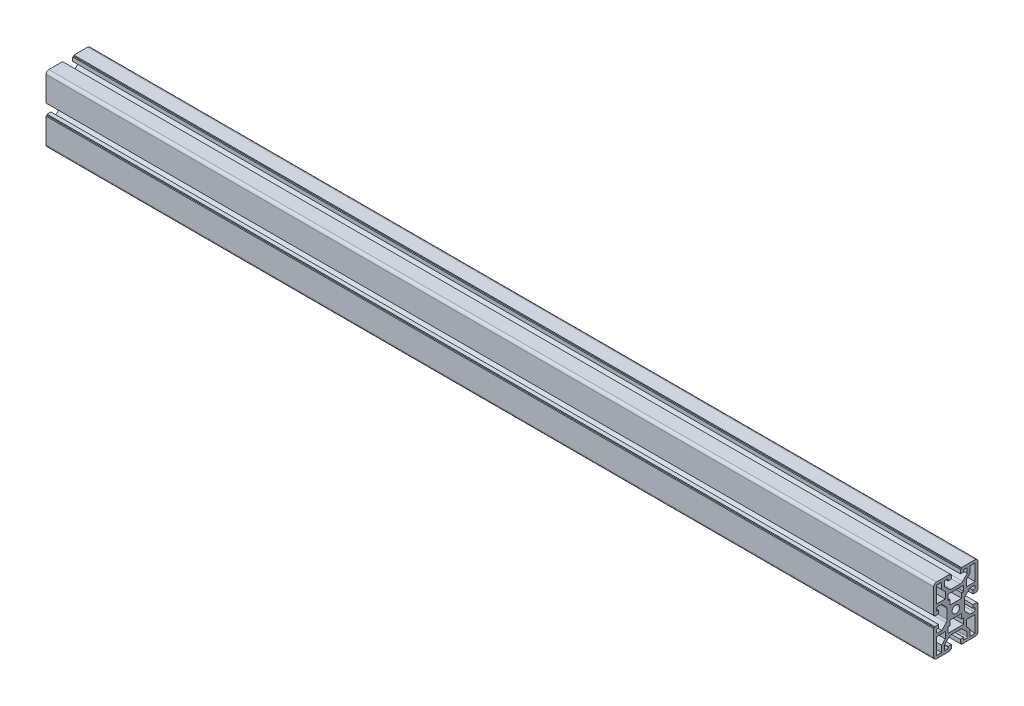
SolidWorks part; units mm, degrees
ref_plane "前视基准面" through (0, 0, 0) normal (0, 0, 1) x (1, 0, 0)
ref_plane "上视基准面" through (0, 0, 0) normal (0, 1, 0) x (1, 0, 0)
ref_plane "右视基准面" through (0, 0, 0) normal (1, 0, 0) x (0, 0, -1)
sketch "草图1" plane through (0, 0, 0) normal (0, 0, 1) x (1, 0, 0)
  line L0 (0, 0) -> (800, 0)
  dimension "D1" = 800
other "4060-a 默认<按加工>(1)"
ref_plane "基准面1" through (0, 0, 0) normal (1, 0, 0) x (0, 1, 0)
sketch "草图19" plane through (0, 0, 0) normal (1, 0, 0) x (0, 1, 0)
  line L0 (27.5, -12.75) -> (27.5, -17.5)
  line L1 (27.5, -17.5) -> (12.75, -17.5)
  line L2 (12.75, -17.5) -> (12.75, -9.5)
  line L3 (12.75, -9.5) -> (18.462, -9.5)
  line L4 (18.462, -9.5) -> (21.7348, -12.75)
  line L5 (21.7348, -12.75) -> (27.5, -12.75)
  line L6 (5.9, 5.25) -> (10.25, 5.25)
  line L7 (10.25, 5.25) -> (10.25, 7)
  line L8 (10.25, 7) -> (15.25, 7)
  line L9 (15.25, 7) -> (15.25, -7)
  line L10 (15.25, -7) -> (10.25, -7)
  line L11 (10.25, -7) -> (10.25, -5.25)
  line L12 (10.25, -5.25) -> (5.9, -5.25)
  line L13 (5.9, -5.25) -> (5.9, 5.25)
  line L14 (-27.5, 12.75) -> (-27.5, 17.5)
  line L15 (-27.5, 17.5) -> (-12.75, 17.5)
  line L16 (-12.75, 17.5) -> (-12.75, 9.5)
  line L17 (-12.75, 9.5) -> (-18.462, 9.5)
  line L18 (-18.462, 9.5) -> (-21.7348, 12.75)
  line L19 (-21.7348, 12.75) -> (-27.5, 12.75)
  line L20 (27.5, 17.5) -> (27.5, 12.75)
  line L21 (27.5, 12.75) -> (21.7348, 12.75)
  line L22 (21.7348, 12.75) -> (18.462, 9.5)
  line L23 (18.462, 9.5) -> (12.75, 9.5)
  line L24 (12.75, 9.5) -> (12.75, 17.5)
  line L25 (12.75, 17.5) -> (27.5, 17.5)
  line L26 (-10.25, 7) -> (-10.25, 5.25)
  line L27 (-10.25, 5.25) -> (-5.9, 5.25)
  line L28 (-5.9, 5.25) -> (-5.9, -5.25)
  line L29 (-5.9, -5.25) -> (-10.25, -5.25)
  line L30 (-10.25, -5.25) -> (-10.25, -7)
  line L31 (-10.25, -7) -> (-15.25, -7)
  line L32 (-15.25, -7) -> (-15.25, 7)
  line L33 (-15.25, 7) -> (-10.25, 7)
  line L34 (-27.5, -17.5) -> (-27.5, -12.75)
  line L35 (-27.5, -12.75) -> (-21.7348, -12.75)
  line L36 (-21.7348, -12.75) -> (-18.462, -9.5)
  line L37 (-18.462, -9.5) -> (-12.75, -9.5)
  line L38 (-12.75, -9.5) -> (-12.75, -17.5)
  line L39 (-12.75, -17.5) -> (-27.5, -17.5)
  line L40 (10.25, 16.5) -> (10.25, 12.7652)
  line L41 (10.25, 12.7652) -> (6.1496, 8.6361)
  line L42 (4.0209, 7.75) -> (-4.0209, 7.75)
  line L43 (-6.1496, 8.6361) -> (-10.25, 12.7652)
  line L44 (-10.25, 12.7652) -> (-10.25, 16.5)
  line L45 (-9.25, 17.5) -> (-8, 17.5)
  line L46 (-7, 16.5) -> (-7, 15.5)
  line L47 (-7, 15.5) -> (-4.1, 15.5)
  line L48 (-4.1, 15.5) -> (-4.1, 19)
  line L49 (-4.1, 19) -> (-5.1, 19)
  line L50 (-5.1, 19) -> (-5.1, 20)
  line L51 (-5.1, 20) -> (-27.5, 20)
  line L52 (-30, 17.5) -> (-30, 5.1)
  line L53 (-30, 5.1) -> (-29, 5.1)
  line L54 (-29, 5.1) -> (-29, 4.1)
  line L55 (-29, 4.1) -> (-25.5, 4.1)
  line L56 (-25.5, 4.1) -> (-25.5, 7)
  line L57 (-25.5, 7) -> (-26.5, 7)
  line L58 (-27.5, 8) -> (-27.5, 9.25)
  line L59 (-26.5, 10.25) -> (-22.7652, 10.25)
  line L60 (-22.7652, 10.25) -> (-18.6361, 6.1496)
  line L61 (-17.75, 4.0209) -> (-17.75, -4.0209)
  line L62 (-18.6361, -6.1496) -> (-22.7652, -10.25)
  line L63 (-22.7652, -10.25) -> (-26.5, -10.25)
  line L64 (-27.5, -9.25) -> (-27.5, -8)
  line L65 (-26.5, -7) -> (-25.5, -7)
  line L66 (-25.5, -7) -> (-25.5, -4.1)
  line L67 (-25.5, -4.1) -> (-29, -4.1)
  line L68 (-29, -4.1) -> (-29, -5.1)
  line L69 (-29, -5.1) -> (-30, -5.1)
  line L70 (-30, -5.1) -> (-30, -17.5)
  line L71 (-27.5, -20) -> (-5.1, -20)
  line L72 (-5.1, -20) -> (-5.1, -19)
  line L73 (-5.1, -19) -> (-4.1, -19)
  line L74 (-4.1, -19) -> (-4.1, -15.5)
  line L75 (-4.1, -15.5) -> (-7, -15.5)
  line L76 (-7, -15.5) -> (-7, -16.5)
  line L77 (-8, -17.5) -> (-9.25, -17.5)
  line L78 (-10.25, -16.5) -> (-10.25, -12.7652)
  line L79 (-10.25, -12.7652) -> (-6.1496, -8.6361)
  line L80 (-4.0209, -7.75) -> (4.0209, -7.75)
  line L81 (6.1496, -8.6361) -> (10.25, -12.7652)
  line L82 (10.25, -12.7652) -> (10.25, -16.5)
  line L83 (9.25, -17.5) -> (8, -17.5)
  line L84 (7, -16.5) -> (7, -15.5)
  line L85 (7, -15.5) -> (4.1, -15.5)
  line L86 (4.1, -15.5) -> (4.1, -19)
  line L87 (4.1, -19) -> (5.1, -19)
  line L88 (5.1, -19) -> (5.1, -20)
  line L89 (5.1, -20) -> (27.5, -20)
  line L90 (30, -17.5) -> (30, -5.1)
  line L91 (30, -5.1) -> (29, -5.1)
  line L92 (29, -5.1) -> (29, -4.1)
  line L93 (29, -4.1) -> (25.5, -4.1)
  line L94 (25.5, -4.1) -> (25.5, -7)
  line L95 (25.5, -7) -> (26.5, -7)
  line L96 (27.5, -8) -> (27.5, -9.25)
  line L97 (26.5, -10.25) -> (22.7652, -10.25)
  line L98 (22.7652, -10.25) -> (18.6361, -6.1496)
  line L99 (17.75, -4.0209) -> (17.75, 4.0209)
  line L100 (18.6361, 6.1496) -> (22.7652, 10.25)
  line L101 (22.7652, 10.25) -> (26.5, 10.25)
  line L102 (27.5, 9.25) -> (27.5, 8)
  line L103 (26.5, 7) -> (25.5, 7)
  line L104 (25.5, 7) -> (25.5, 4.1)
  line L105 (25.5, 4.1) -> (29, 4.1)
  line L106 (29, 4.1) -> (29, 5.1)
  line L107 (29, 5.1) -> (30, 5.1)
  line L108 (30, 5.1) -> (30, 17.5)
  line L109 (27.5, 20) -> (5.1, 20)
  line L110 (5.1, 20) -> (5.1, 19)
  line L111 (5.1, 19) -> (4.1, 19)
  line L112 (4.1, 19) -> (4.1, 15.5)
  line L113 (4.1, 15.5) -> (7, 15.5)
  line L114 (7, 15.5) -> (7, 16.5)
  line L115 (8, 17.5) -> (9.25, 17.5)
  arc A0 (6.1496, 8.6361) -> (4.0209, 7.75) centre (4.0209, 10.75) cw
  arc A1 (-4.0209, 7.75) -> (-6.1496, 8.6361) centre (-4.0209, 10.75) cw
  arc A2 (-10.25, 16.5) -> (-9.25, 17.5) centre (-9.25, 16.5) cw
  arc A3 (-8, 17.5) -> (-7, 16.5) centre (-8, 16.5) cw
  arc A4 (-27.5, 20) -> (-30, 17.5) centre (-27.5, 17.5) ccw
  arc A5 (-26.5, 7) -> (-27.5, 8) centre (-26.5, 8) cw
  arc A6 (-27.5, 9.25) -> (-26.5, 10.25) centre (-26.5, 9.25) cw
  arc A7 (-18.6361, 6.1496) -> (-17.75, 4.0209) centre (-20.75, 4.0209) cw
  arc A8 (-17.75, -4.0209) -> (-18.6361, -6.1496) centre (-20.75, -4.0209) cw
  arc A9 (-26.5, -10.25) -> (-27.5, -9.25) centre (-26.5, -9.25) cw
  arc A10 (-27.5, -8) -> (-26.5, -7) centre (-26.5, -8) cw
  arc A11 (-30, -17.5) -> (-27.5, -20) centre (-27.5, -17.5) ccw
  arc A12 (-7, -16.5) -> (-8, -17.5) centre (-8, -16.5) cw
  arc A13 (-9.25, -17.5) -> (-10.25, -16.5) centre (-9.25, -16.5) cw
  arc A14 (-6.1496, -8.6361) -> (-4.0209, -7.75) centre (-4.0209, -10.75) cw
  arc A15 (4.0209, -7.75) -> (6.1496, -8.6361) centre (4.0209, -10.75) cw
  arc A16 (10.25, -16.5) -> (9.25, -17.5) centre (9.25, -16.5) cw
  arc A17 (8, -17.5) -> (7, -16.5) centre (8, -16.5) cw
  arc A18 (27.5, -20) -> (30, -17.5) centre (27.5, -17.5) ccw
  arc A19 (26.5, -7) -> (27.5, -8) centre (26.5, -8) cw
  arc A20 (27.5, -9.25) -> (26.5, -10.25) centre (26.5, -9.25) cw
  arc A21 (18.6361, -6.1496) -> (17.75, -4.0209) centre (20.75, -4.0209) cw
  arc A22 (17.75, 4.0209) -> (18.6361, 6.1496) centre (20.75, 4.0209) cw
  arc A23 (26.5, 10.25) -> (27.5, 9.25) centre (26.5, 9.25) cw
  arc A24 (27.5, 8) -> (26.5, 7) centre (26.5, 8) cw
  arc A25 (30, 17.5) -> (27.5, 20) centre (27.5, 17.5) ccw
  arc A26 (7, 16.5) -> (8, 17.5) centre (8, 16.5) cw
  arc A27 (9.25, 17.5) -> (10.25, 16.5) centre (9.25, 16.5) cw
  circle A28 centre (0, 0) radius 3.4
  point P170 (0, 0)
sketch "草图14" plane through (0, -12.75, 0) normal (0, -1, 0) x (-1, 0, 0)
  line L0 (0, 0) -> (-800, 0) construction
  line L2 (-800, -17.5) -> (-800, -9.5) construction
  line L3 (1200, -3.15) -> (0, -3.15) construction
  circle A0 centre (-785, 0) radius 3
  dimension "D1" = 6
  dimension "D2" = 3.15
  dimension "D3" = 15
extrude "切除-拉伸1" cut sketch "草图14" against normal blind 10
